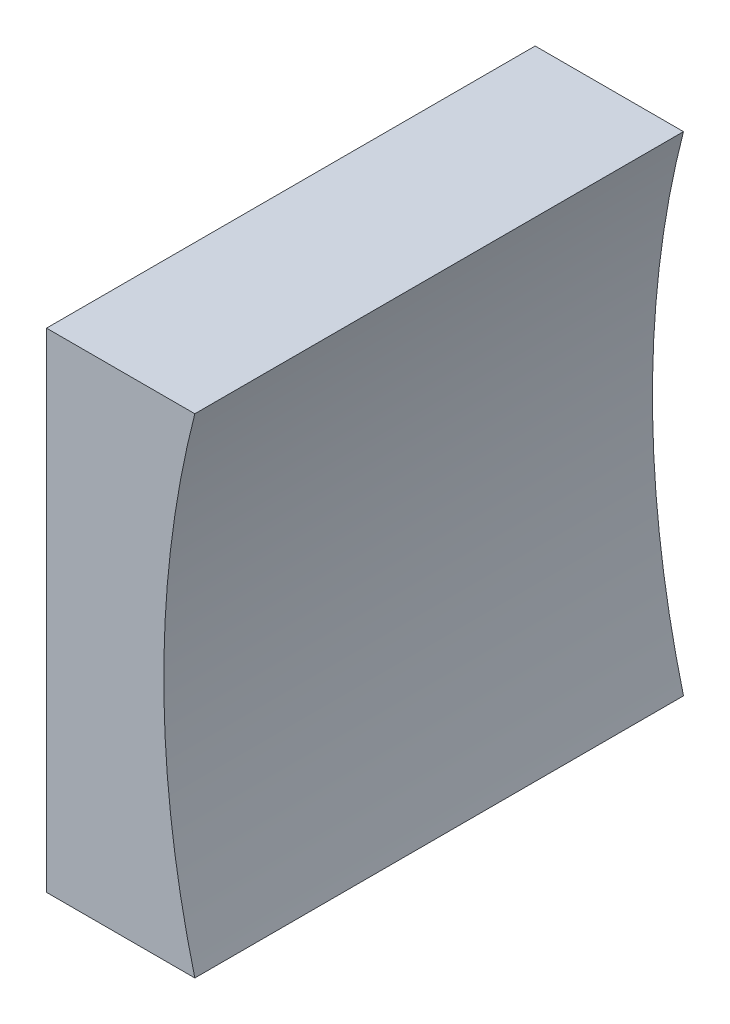
SolidWorks part; units mm, degrees
ref_plane "前视基准面" through (0, 0, 0) normal (0, 0, 1) x (1, 0, 0)
ref_plane "上视基准面" through (0, 0, 0) normal (0, 1, 0) x (1, 0, 0)
ref_plane "右视基准面" through (0, 0, 0) normal (1, 0, 0) x (0, 0, -1)
sketch "草图1" plane through (0, 0, 0) normal (0, 0, 1) x (1, 0, 0)
  line L0 (139.3275, 33.429) -> (149.0915, 33.429) construction
  line L1 (142.3536, 33.429) -> (142.3536, 39.679)
  line L2 (142.3536, 39.679) -> (146.1474, 39.679)
  line L3 (146.1474, 27.179) -> (142.3536, 27.179)
  line L4 (142.3536, 27.179) -> (142.3536, 33.429)
  arc A0 (146.1474, 39.679) -> (146.1474, 27.179) centre (170.3536, 33.429) ccw
  dimension "D1" = 25
  dimension "D2" = 3.7939
extrude "凸台-拉伸1" add sketch "草图1" along normal blind 12.5
